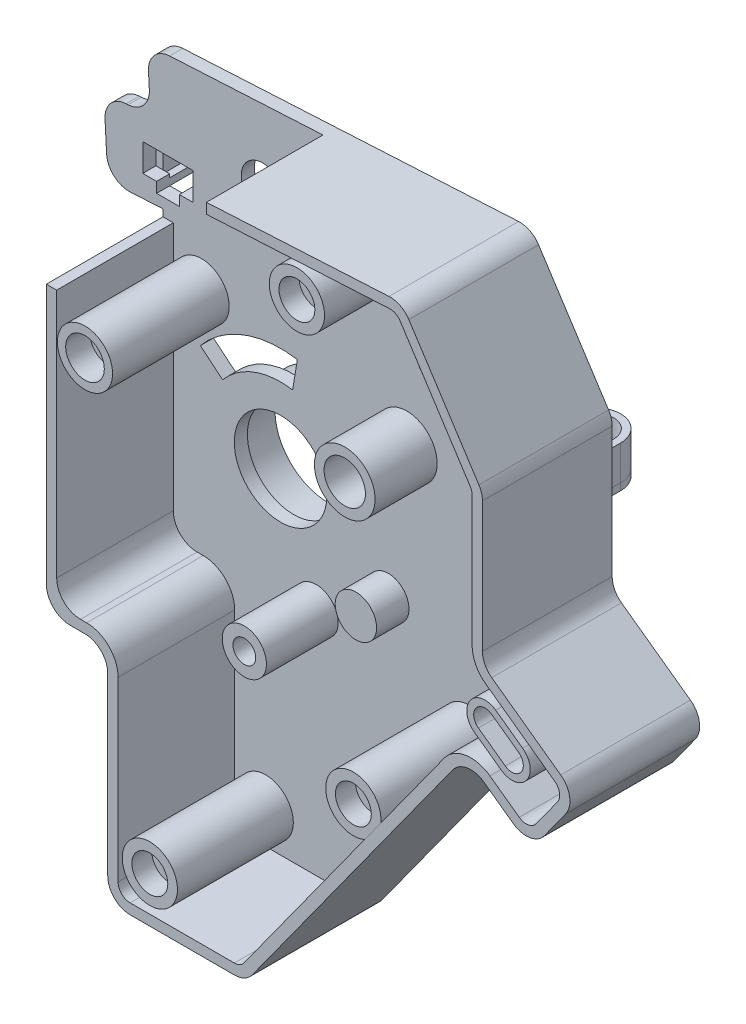
SolidWorks part; units mm, degrees
ref_plane "Front Plane" through (0, 0, 0) normal (0, 0, 1) x (1, 0, 0)
ref_plane "Top Plane" through (0, 0, 0) normal (0, 1, 0) x (1, 0, 0)
ref_plane "Right Plane" through (0, 0, 0) normal (1, 0, 0) x (0, 0, -1)
sketch "Sketch1" plane through (0, 0, 0) normal (0, 0, 1) x (1, 0, 0)
  line L34 (3.24, 0) -> (18.3427, 0)
  line L35 (20.9699, 1.3438) -> (49.9994, 41.5647)
  line L36 (54.5228, 42.2957) -> (58.7717, 39.229)
  line L37 (63.2951, 39.96) -> (66.3851, 44.2413)
  line L38 (65.6541, 48.7647) -> (55.6621, 55.9765)
  line L39 (54.3183, 58.6037) -> (54.3183, 77.4885)
  line L40 (53.7975, 79.2503) -> (43.6473, 94.916)
  line L41 (0, 3.24) -> (0, 32)
  line L48 (-11.1707, 93.6047) -> (40.7546, 96.3896)
  line L49 (0, 32) -> (-8.9, 32)
  line L50 (-8.9, 32) -> (-8.9, 59.47)
  line L54 (-11.1707, 93.6047) -> (-10.6994, 84.8173)
  line L55 (-10.6994, 84.8173) -> (-17.4697, 84.4542)
  line L56 (-17.4697, 84.4542) -> (-16.8913, 73.6697)
  line L57 (-8.9, 59.47) -> (-8.9, 74.0983)
  line L58 (-8.9, 74.0983) -> (-16.8913, 73.6697)
  arc A2 (3.24, 0) -> (0, 3.24) centre (3.24, 3.24) cw
  arc A3 (18.3427, 0) -> (20.9699, 1.3438) centre (18.3427, 3.24) ccw
  arc A4 (49.9994, 41.5647) -> (54.5228, 42.2957) centre (52.6266, 39.6685) cw
  arc A5 (58.7717, 39.229) -> (63.2951, 39.96) centre (60.6679, 41.8562) ccw
  arc A6 (66.3851, 44.2413) -> (65.6541, 48.7647) centre (63.758, 46.1375) ccw
  arc A7 (55.6621, 55.9765) -> (54.3183, 58.6037) centre (57.5583, 58.6037) cw
  arc A8 (54.3183, 77.4885) -> (53.7975, 79.2503) centre (51.0783, 77.4885) ccw
  arc A9 (43.6473, 94.916) -> (40.7546, 96.3896) centre (40.9282, 93.1543) ccw
  point P24 (0, 0)
  point P27 (20, 0)
  point P30 (51.8956, 44.1918)
  point P33 (61.3989, 37.3328)
  point P36 (68.2813, 46.8685)
  point P39 (54.3183, 56.9464)
  point P42 (54.3183, 78.4464)
  point P45 (42.6275, 96.49)
  dimension "D5" = 11.76
  dimension "D13" = 10.8
  dimension "D18" = 8.9
  dimension "D20" = 8.0028
  dimension "D1" = 20
  dimension "D2" = 54.5
  dimension "D3" = 125.82
  dimension "D4" = 11.72
  dimension "D6" = 17.22
  dimension "D7" = 21.5
  dimension "D8" = 21.5
  dimension "D9" = 32
  dimension "D10" = 27.47
  dimension "D12" = 8.8
  dimension "D14" = 119.87
  dimension "D15" = 52
  dimension "D16" = 147.06
  dimension "D19" = 6.78
extrude "Boss-Extrude1" add sketch "Sketch1" along normal blind 1.9
sketch "Sketch16" plane through (0, 0, 1.9) normal (0, 0, 1) x (1, 0, 0)
  line L0 (-15.8915, 83.0367) -> (-15.4738, 75.2479)
  line L1 (-15.4738, 75.2479) -> (-7.4, 75.6809)
  line L2 (-7.4, 75.6809) -> (-7.4, 33.5)
  line L3 (-7.4, 33.5) -> (1.5, 33.5)
  line L4 (1.5, 33.5) -> (1.5, 3.24)
  line L5 (3.24, 1.5) -> (18.3427, 1.5)
  line L6 (19.7536, 2.2217) -> (48.7832, 42.4425)
  line L7 (55.4007, 43.512) -> (59.6496, 40.4453)
  line L8 (62.0788, 40.8379) -> (65.1689, 45.1192)
  line L9 (64.7763, 47.5484) -> (54.7843, 54.7602)
  line L10 (52.8183, 58.6037) -> (52.8183, 77.4885)
  line L11 (52.5386, 78.4346) -> (42.3884, 94.1004)
  line L12 (40.835, 94.8918) -> (-9.5925, 92.1872)
  line L13 (-9.5925, 92.1872) -> (-9.1213, 83.3998)
  line L14 (-9.1213, 83.3998) -> (-15.8915, 83.0367)
  line L15 (-8.9, 74.0983) -> (-8.9, 32)
  line L16 (-8.9, 32) -> (0, 32)
  line L17 (0, 32) -> (0, 3.24)
  line L18 (3.24, 0) -> (18.3427, 0)
  line L19 (20.9699, 1.3438) -> (49.9994, 41.5647)
  line L20 (54.5228, 42.2957) -> (58.7717, 39.229)
  line L21 (63.2951, 39.96) -> (66.3851, 44.2413)
  line L22 (65.6541, 48.7647) -> (55.6621, 55.9765)
  line L23 (54.3183, 58.6037) -> (54.3183, 77.4885)
  line L24 (53.7975, 79.2503) -> (43.6473, 94.916)
  line L25 (40.7546, 96.3896) -> (-11.1707, 93.6047)
  line L26 (-11.1707, 93.6047) -> (-10.6994, 84.8173)
  line L27 (-10.6994, 84.8173) -> (-17.4697, 84.4542)
  line L28 (-17.4697, 84.4542) -> (-16.8913, 73.6697)
  line L29 (-16.8913, 73.6697) -> (-8.9, 74.0983)
  line L30 (-8.9, 74.0983) -> (-8.9, 32)
  line L31 (-8.9, 32) -> (0, 32)
  line L32 (0, 32) -> (0, 3.24)
  line L33 (3.24, 0) -> (18.3427, 0)
  line L34 (20.9699, 1.3438) -> (49.9994, 41.5647)
  line L35 (54.5228, 42.2957) -> (58.7717, 39.229)
  line L36 (63.2951, 39.96) -> (66.3851, 44.2413)
  line L37 (65.6541, 48.7647) -> (55.6621, 55.9765)
  line L38 (54.3183, 58.6037) -> (54.3183, 77.4885)
  line L39 (53.7975, 79.2503) -> (43.6473, 94.916)
  line L40 (40.7546, 96.3896) -> (-11.1707, 93.6047)
  line L41 (-11.1707, 93.6047) -> (-10.6994, 84.8173)
  line L42 (-10.6994, 84.8173) -> (-17.4697, 84.4542)
  line L43 (-17.4697, 84.4542) -> (-16.8913, 73.6697)
  line L44 (-16.8913, 73.6697) -> (-8.9, 74.0983)
  arc A0 (1.5, 3.24) -> (3.24, 1.5) centre (3.24, 3.24) ccw
  arc A1 (18.3427, 1.5) -> (19.7536, 2.2217) centre (18.3427, 3.24) ccw
  arc A2 (55.4007, 43.512) -> (48.7832, 42.4425) centre (52.6266, 39.6685) ccw
  arc A3 (59.6496, 40.4453) -> (62.0788, 40.8379) centre (60.6679, 41.8562) ccw
  arc A4 (65.1689, 45.1192) -> (64.7763, 47.5484) centre (63.758, 46.1375) ccw
  arc A5 (52.8183, 58.6037) -> (54.7843, 54.7602) centre (57.5583, 58.6037) ccw
  arc A6 (52.8183, 77.4885) -> (52.5386, 78.4346) centre (51.0783, 77.4885) ccw
  arc A7 (42.3884, 94.1004) -> (40.835, 94.8918) centre (40.9282, 93.1543) ccw
  arc A8 (0, 3.24) -> (3.24, 0) centre (3.24, 3.24) ccw
  arc A9 (18.3427, 0) -> (20.9699, 1.3438) centre (18.3427, 3.24) ccw
  arc A10 (54.5228, 42.2957) -> (49.9994, 41.5647) centre (52.6266, 39.6685) ccw
  arc A11 (58.7717, 39.229) -> (63.2951, 39.96) centre (60.6679, 41.8562) ccw
  arc A12 (66.3851, 44.2413) -> (65.6541, 48.7647) centre (63.758, 46.1375) ccw
  arc A13 (54.3183, 58.6037) -> (55.6621, 55.9765) centre (57.5583, 58.6037) ccw
  arc A14 (54.3183, 77.4885) -> (53.7975, 79.2503) centre (51.0783, 77.4885) ccw
  arc A15 (43.6473, 94.916) -> (40.7546, 96.3896) centre (40.9282, 93.1543) ccw
  arc A16 (0, 3.24) -> (3.24, 0) centre (3.24, 3.24) ccw
  arc A17 (18.3427, 0) -> (20.9699, 1.3438) centre (18.3427, 3.24) ccw
  arc A18 (54.5228, 42.2957) -> (49.9994, 41.5647) centre (52.6266, 39.6685) ccw
  arc A19 (58.7717, 39.229) -> (63.2951, 39.96) centre (60.6679, 41.8562) ccw
  arc A20 (66.3851, 44.2413) -> (65.6541, 48.7647) centre (63.758, 46.1375) ccw
  arc A21 (54.3183, 58.6037) -> (55.6621, 55.9765) centre (57.5583, 58.6037) ccw
  arc A22 (54.3183, 77.4885) -> (53.7975, 79.2503) centre (51.0783, 77.4885) ccw
  arc A23 (43.6473, 94.916) -> (40.7546, 96.3896) centre (40.9282, 93.1543) ccw
  dimension "D1" = 0
  dimension "D2" = 1.5
extrude "Boss-Extrude8" add sketch "Sketch16" along normal blind 16.9
sketch "Sketch6" plane through (0, 0, 1.9) normal (0, 0, 1) x (1, 0, 0)
  circle A0 centre (6, 6.5) radius 4
  circle A1 centre (6, 6.5) radius 2.6
  circle A2 centre (35.5, 30) radius 4
  circle A3 centre (35.5, 30) radius 2.6
  circle A4 centre (27.32, 89.23) radius 4
  circle A7 centre (27.32, 89.23) radius 2.6
  dimension "D3" = 8
  dimension "D4" = 5.2
  dimension "D7" = 8
  dimension "D8" = 5.2
  dimension "D11" = 8
  dimension "D12" = 5.2
  dimension "D2" = 6
  dimension "D1" = 6.5
  dimension "D5" = 35.5
  dimension "D6" = 30
  dimension "D9" = 27.32
  dimension "D10" = 89.23
extrude "Boss-Extrude3" add sketch "Sketch6" along normal blind 16.8
sketch "Sketch8" plane through (0, 0, 1.9) normal (0, 0, 1) x (1, 0, 0)
  line L0 (10.5808, 64.9132) -> (9.9052, 60.7679)
  line L1 (-0.2479, 56.9644) -> (-3.4809, 59.6455)
  line L3 (-7.55, 63.02) -> (8.15, 50) construction
  line L4 (0, 0) -> (8.15, 50) construction
  line L5 (8.15, 50) -> (10.9104, 66.9353) construction
  line L6 (20.9463, 50) -> (-15.5457, 50) construction
  line L7 (54.3183, 58.6037) -> (54.3183, 77.4885) construction
  circle A0 centre (8.15, 50) radius 6.71
  circle A1 centre (5.55, 83.99) radius 3.1
  arc A2 (9.9052, 60.7679) -> (-0.2479, 56.9644) centre (8.15, 50) ccw
  arc A3 (10.5808, 64.9132) -> (-3.4809, 59.6455) centre (8.15, 50) ccw
  circle A4 centre (32.5683, 75.4) radius 5
  circle A5 centre (35.5, 30) radius 2.6 construction
  point P11 (-7.55, 63.02)
  dimension "D3" = 13.42
  dimension "D6" = 6.2
  dimension "D7" = 4.2
  dimension "D8" = 4.2
  dimension "D10" = 45.4
  dimension "D12" = 10
  dimension "D1" = 50
  dimension "D2" = 8.15
  dimension "D4" = 5.55
  dimension "D5" = 83.99
  dimension "D9" = 15.7
  dimension "D11" = 21.75
  dimension "D13" = 39.669
extrude "Cut-Extrude2" cut sketch "Sketch8" against normal up to surface (1.9 mm away) up to face at (27.395, 52.0581, 0)
sketch "Sketch9" plane through (0, 0, 1.9) normal (0, 0, 1) x (1, 0, 0)
  circle A0 centre (26.45, 62) radius 4.4
  circle A1 centre (26.45, 62) radius 3
  circle A3 centre (26.45, 62) radius 1.375 construction
  dimension "D1" = 8.8
  dimension "D4" = 6
extrude "Boss-Extrude4" add sketch "Sketch9" along normal blind 9
sketch "Sketch10" plane through (0, 0, 1.9) normal (0, 0, 1) x (1, 0, 0)
  circle A0 centre (23.77, 41.68) radius 3
  circle A2 centre (23.77, 41.68) radius 2 construction
  dimension "D1" = 6
extrude "Boss-Extrude5" add sketch "Sketch10" along normal blind 4.7
sketch "Sketch11" plane through (0, 0, 1.9) normal (0, 0, 1) x (1, 0, 0)
  circle A0 centre (13.3, 34.85) radius 3.2
  circle A1 centre (13.3, 34.85) radius 1.65
  circle A3 centre (13.3, 34.85) radius 3 construction
  dimension "D1" = 6.4
  dimension "D4" = 3.3
extrude "Boss-Extrude6" add sketch "Sketch11" along normal blind 10.4
sketch "Sketch12" plane through (0, 0, 1.9) normal (0, 0, 1) x (1, 0, 0)
  circle A0 centre (-3.3, 66.65) radius 4
  dimension "D1" = 8
  dimension "D3" = 3.3
  dimension "D2" = 66.65
extrude "Boss-Extrude7" add sketch "Sketch12" along normal blind 16.9
sketch "Sketch13" plane through (0, 0, 18.8) normal (0, 0, 1) x (1, 0, 0)
  circle A0 centre (-3.3, 66.65) radius 2.8
  dimension "D1" = 5.6
extrude "Cut-Extrude3" cut sketch "Sketch13" against normal blind 3.5
sketch "Sketch14" plane through (0, 0, 1.9) normal (0, 0, 1) x (1, 0, 0)
  line L0 (44.25, 71.49) -> (51.55, 71.49)
  line L1 (51.55, 71.49) -> (51.55, 67.49)
  line L2 (51.55, 67.49) -> (49.55, 67.49)
  line L3 (49.55, 67.49) -> (49.55, 65.99)
  line L4 (49.55, 65.99) -> (46.25, 65.99)
  line L5 (46.25, 65.99) -> (46.25, 67.49)
  line L6 (46.25, 67.49) -> (44.25, 67.49)
  line L7 (44.25, 67.49) -> (44.25, 71.49)
  line L8 (-11.82, 81.09) -> (-4.52, 81.09)
  line L9 (-4.52, 81.09) -> (-4.52, 77.09)
  line L10 (-4.52, 77.09) -> (-6.52, 77.09)
  line L11 (-6.52, 77.09) -> (-6.52, 75.59)
  line L12 (-6.52, 75.59) -> (-9.82, 75.59)
  line L13 (-9.82, 75.59) -> (-9.82, 77.09)
  line L14 (-9.82, 77.09) -> (-11.82, 77.09)
  line L15 (-11.82, 77.09) -> (-11.82, 81.09)
  dimension "D1" = 2
  dimension "D2" = 2
  dimension "D3" = 46.25
  dimension "D4" = 65.99
  dimension "D5" = 4
  dimension "D6" = 7.3
  dimension "D7" = 5.5
  dimension "D8" = 7.3
  dimension "D9" = 6.52
  dimension "D10" = 75.59
  dimension "D11" = 4
  dimension "D12" = 5.5
sketch "Sketch17" plane through (0, 0, 18.8) normal (0, 0, 1) x (1, 0, 0)
  line L0 (-8.9, 73.0983) -> (-7.4, 73.0983)
  line L1 (-8.9, 74.0983) -> (-8.9, 32) construction
  line L2 (-7.4, 75.6809) -> (-7.4, 33.5) construction
  line L3 (40.7546, 96.3896) -> (-11.1707, 93.6047) construction
  line L4 (40.835, 94.8918) -> (-9.5925, 92.1872) construction
  line L5 (-11.1707, 93.6047) -> (-10.6994, 84.8173) construction
  line L6 (-17.4697, 84.4542) -> (-16.8913, 73.6697) construction
  line L7 (-10.6994, 84.8173) -> (-17.4697, 84.4542) construction
  line L8 (-9.5925, 92.1872) -> (-9.1213, 83.3998) construction
  line L9 (-9.1213, 83.3998) -> (-15.8915, 83.0367) construction
  line L10 (-15.8915, 83.0367) -> (-15.4738, 75.2479) construction
  line L11 (-15.4738, 75.2479) -> (-7.4, 75.6809) construction
  line L12 (10.7977, 94.7829) -> (-11.1707, 93.6047)
  line L13 (10.7977, 93.2808) -> (-9.5925, 92.1872)
  line L14 (-11.1707, 93.6047) -> (-10.6994, 84.8173)
  line L15 (-17.4697, 84.4542) -> (-16.8913, 73.6697)
  line L16 (-10.6994, 84.8173) -> (-17.4697, 84.4542)
  line L17 (-9.5925, 92.1872) -> (-9.1213, 83.3998)
  line L18 (-9.1213, 83.3998) -> (-15.8915, 83.0367)
  line L19 (-15.8915, 83.0367) -> (-15.4738, 75.2479)
  line L20 (-15.4738, 75.2479) -> (-7.4, 75.6809)
  line L21 (-7.4, 75.6809) -> (-7.4, 73.0983)
  line L22 (-16.8913, 73.6697) -> (-8.9, 74.0983) construction
  line L23 (-8.9, 74.0983) -> (-8.9, 73.0983)
  line L24 (-16.8913, 73.6697) -> (-8.9, 74.0983)
  line L25 (10.7977, 94.7829) -> (10.7977, 93.2808)
  point P4 (10.7977, 94.7829)
  dimension "D1" = 1
  dimension "D2" = 30
extrude "Cut-Extrude4" cut sketch "Sketch17" against normal blind 16.9
fillet "Fillet1" radius 3.24 1 edges at (-17.4697, 84.4542, 0.95)
fillet "Fillet2" radius 3.24 1 edges at (-10.6994, 84.8173, 0.95)
fillet "Fillet3" radius 3.24 1 edges at (-11.1707, 93.6047, 0.95)
fillet "Fillet4" radius 3.24 1 edges at (-16.8913, 73.6697, 0.95)
fillet "Fillet7" radius 3.45 1 edges at (-8.9, 32, 9.4)
fillet "Fillet8" radius 3.45 1 edges at (-7.4, 33.5, 10.35)
fillet "Fillet9" radius 4.56 1 edges at (1.5, 33.5, 10.35)
fillet "Fillet10" radius 3.33 1 edges at (0, 32, 9.4)
extrude "Cut-Extrude8" cut sketch "Sketch14" against normal blind 10
sketch "Sketch19" plane through (0, 65.99, 0) normal (0, 1, 0) x (1, 0, 0)
  line L0 (46.25, 4) -> (46.25, 0)
  line L1 (49.55, 4) -> (49.55, 0)
  line L2 (44.25, 4) -> (44.25, 0)
  line L3 (51.55, 4) -> (51.55, 0)
  line L4 (44.25, 0) -> (46.25, 0)
  line L5 (49.55, 0) -> (51.55, 0)
  arc A0 (49.55, 4) -> (46.25, 4) centre (47.9, 4) ccw
  arc A1 (51.55, 4) -> (44.25, 4) centre (47.9, 4) ccw
  dimension "D1" = 4
  dimension "D2" = 7.3
extrude "Boss-Extrude9" add sketch "Sketch19" along normal blind 1
sketch "Sketch20" plane through (0, 66.99, 0) normal (0, 1, 0) x (1, 0, 0)
  line L0 (44.25, 0) -> (46.25, 0) construction
  line L1 (49.55, 0) -> (51.55, 0) construction
  line L2 (51.55, 0) -> (51.55, 4) construction
  line L3 (44.25, 4) -> (44.25, 0) construction
  line L4 (44.25, 0) -> (45.25, 0)
  line L5 (50.55, 0) -> (51.55, 0)
  line L6 (51.55, 0) -> (51.55, 4)
  line L7 (44.25, 4) -> (44.25, 0)
  line L8 (45.25, 4) -> (45.25, 0)
  line L9 (50.55, 4) -> (50.55, 0)
  arc A1 (51.55, 4) -> (44.25, 4) centre (47.9, 4) ccw construction
  arc A2 (50.55, 4) -> (45.25, 4) centre (47.9, 4) ccw
  arc A3 (50.55, 4) -> (45.25, 4) centre (47.9, 4) ccw
  arc A4 (51.55, 4) -> (44.25, 4) centre (47.9, 4) ccw
  dimension "D1" = 1
extrude "Boss-Extrude10" add sketch "Sketch20" along normal blind 5 separate body
sketch "Sketch21" plane through (0, 75.59, 0) normal (0, 1, 0) x (1, 0, 0)
  line L0 (-9.82, 4) -> (-9.82, 0)
  line L1 (-6.52, 4) -> (-6.52, 0)
  line L2 (-11.82, 4) -> (-11.82, 0)
  line L3 (-4.52, 4) -> (-4.52, 0)
  line L4 (-11.82, 0) -> (-9.82, 0)
  line L5 (-6.52, 0) -> (-4.52, 0)
  arc A0 (-6.52, 4) -> (-9.82, 4) centre (-8.17, 4) ccw
  arc A1 (-4.52, 4) -> (-11.82, 4) centre (-8.17, 4) ccw
  dimension "D1" = 7.3
  dimension "D2" = 4
extrude "Boss-Extrude11" add sketch "Sketch21" along normal blind 1
sketch "Sketch22" plane through (0, 76.59, 0) normal (0, 1, 0) x (1, 0, 0)
  line L0 (-11.82, 0) -> (-9.82, 0) construction
  line L1 (-6.52, 0) -> (-4.52, 0) construction
  line L2 (-4.52, 0) -> (-4.52, 4) construction
  line L3 (-11.82, 4) -> (-11.82, 0) construction
  line L4 (-11.82, 0) -> (-10.82, 0)
  line L5 (-5.52, 0) -> (-4.52, 0)
  line L6 (-4.52, 0) -> (-4.52, 4)
  line L7 (-11.82, 4) -> (-11.82, 0)
  line L8 (-10.82, 4) -> (-10.82, 0)
  line L9 (-5.52, 4) -> (-5.52, 0)
  arc A1 (-4.52, 4) -> (-11.82, 4) centre (-8.17, 4) ccw construction
  arc A2 (-5.52, 4) -> (-10.82, 4) centre (-8.17, 4) ccw
  arc A3 (-5.52, 4) -> (-10.82, 4) centre (-8.17, 4) ccw
  arc A4 (-4.52, 4) -> (-11.82, 4) centre (-8.17, 4) ccw
  dimension "D1" = 1
extrude "Boss-Extrude12" add sketch "Sketch22" along normal blind 5 separate body
sketch "Sketch23" plane through (10.7977, 0, 0) normal (-1, 0, 0) x (0, 0, 1)
  line L4 (18.8, 93.2808) -> (18.8, 94.7829)
  line L5 (18.8, 94.7829) -> (1.9, 94.7829)
  line L6 (1.9, 94.7829) -> (1.9, 93.2808)
  line L7 (1.9, 93.2808) -> (18.8, 93.2808)
  line L8 (18.8, 93.2808) -> (18.8, 94.7829)
  line L9 (18.8, 94.7829) -> (1.9, 94.7829)
  line L10 (1.9, 94.7829) -> (1.9, 93.2808)
  line L11 (1.9, 93.2808) -> (18.8, 93.2808)
  dimension "D1" = 0
extrude "Cut-Extrude9" cut sketch "Sketch23" against normal blind 2
sketch "Sketch24" plane through (12.7977, 0, 0) normal (-1, 0, 0) x (0, 0, 1)
  line L4 (18.8, 93.388) -> (18.8, 94.7829)
  line L5 (18.8, 94.7829) -> (1.9, 94.7829)
  line L6 (1.9, 94.7829) -> (1.9, 93.388)
  line L7 (1.9, 93.388) -> (18.8, 93.388)
  line L8 (18.8, 93.388) -> (18.8, 94.7829)
  line L9 (18.8, 94.7829) -> (1.9, 94.7829)
  line L10 (1.9, 94.7829) -> (1.9, 93.388)
  line L11 (1.9, 93.388) -> (18.8, 93.388)
  dimension "D1" = 0
sketch "Sketch25" plane through (0, 0, 18.8) normal (0, 0, 1) x (1, 0, 0)
  line L0 (12.7977, 94.7829) -> (12.7977, 94.8902)
  line L1 (40.7546, 96.3896) -> (10.7977, 94.7829) construction
  line L2 (12.7977, 94.8902) -> (10.7977, 94.7829)
  line L3 (10.7977, 94.7829) -> (12.7977, 94.7829)
extrude "Cut-Extrude11" cut sketch "Sketch25" against normal up to surface (16.9 mm away) up to face at (8.6, 6.5, 1.9)
sketch "Sketch26" plane through (12.7977, 0, 0) normal (-1, 0, 0) x (0, 0, 1)
  line L4 (18.8, 93.388) -> (18.8, 94.8902)
  line L5 (18.8, 94.8902) -> (1.9, 94.8902)
  line L6 (1.9, 94.8902) -> (1.9, 93.388)
  line L7 (1.9, 93.388) -> (18.8, 93.388)
  line L8 (18.8, 93.388) -> (18.8, 95.9949)
  line L9 (18.8, 95.9949) -> (1.9, 95.9949)
  line L10 (1.9, 95.9949) -> (1.9, 93.388)
  line L11 (1.9, 93.388) -> (18.8, 93.388)
  dimension "D1" = 0
extrude "Cut-Extrude12" cut sketch "Sketch26" against normal blind 1.5
sketch "Sketch27" plane through (0, 0, 0) normal (0, 0, -1) x (-1, 0, 0)
  circle A0 centre (-8.15, 50) radius 6.71 construction
  circle A1 centre (-8.15, 50) radius 6.71
  circle A2 centre (-8.15, 50) radius 7.71
  circle A3 centre (-8.15, 50) radius 8.71
  dimension "D1" = 1
  dimension "D2" = 1
extrude "Boss-Extrude13" add sketch "Sketch27" along normal blind 5 contours A3 A2
sketch "Sketch28" plane through (0, 0, 1.9) normal (0, 0, 1) x (1, 0, 0)
  circle A0 centre (6, 6.5) radius 2.6 construction
  circle A1 centre (27.32, 89.23) radius 2.6
  circle A2 centre (27.32, 89.23) radius 2.6
  circle A3 centre (6, 6.5) radius 2.6
  circle A4 centre (35.5, 30) radius 2.6 construction
  circle A5 centre (35.5, 30) radius 2.6
  dimension "D1" = 0
extrude "Cut-Extrude13" cut sketch "Sketch28" against normal blind 10
ref_plane "Plane1" through (0, 0, 15.8) normal (0, 0, 1) x (1, 0, 0)
sketch "Sketch30" plane through (0, 0, 15.8) normal (0, 0, 1) x (1, 0, 0)
  line L0 (37.184, 26.3718) -> (39.474, 29.5445) construction
  line L1 (37.184, 26.3718) -> (39.474, 29.5445)
  circle A1 centre (27.32, 89.23) radius 1.3
  circle A3 centre (6, 6.5) radius 1.3
  circle A5 centre (35.5, 30) radius 1.3
  circle A6 centre (6, 6.5) radius 4 construction
  circle A8 centre (27.32, 89.23) radius 4 construction
  arc A9 (39.474, 29.5445) -> (37.184, 26.3718) centre (35.5, 30) ccw construction
  circle A10 centre (27.32, 89.23) radius 4
  arc A11 (39.474, 29.5445) -> (37.184, 26.3718) centre (35.5, 30) ccw
  circle A12 centre (6, 6.5) radius 4
  dimension "D1" = 2.6
  dimension "D2" = 2.6
  dimension "D3" = 2.6
extrude "Boss-Extrude14" add sketch "Sketch30" against normal blind 1
sketch "Sketch31" plane through (0, 0, 1.9) normal (0, 0, 1) x (1, 0, 0)
  line L0 (54.4948, 49.8264) -> (58.3869, 47.0173) construction
  line L1 (55.4605, 51.1643) -> (59.3526, 48.3552)
  line L2 (53.5292, 48.4885) -> (57.4213, 45.6793)
  line L3 (65.6541, 48.7647) -> (55.6621, 55.9765) construction
  line L4 (63.2951, 39.96) -> (66.3851, 44.2413) construction
  line L5 (56.0457, 51.9752) -> (59.9378, 49.166)
  line L6 (52.9439, 47.6776) -> (56.8361, 44.8685)
  arc A0 (55.4605, 51.1643) -> (53.5292, 48.4885) centre (54.4948, 49.8264) ccw
  arc A1 (57.4213, 45.6793) -> (59.3526, 48.3552) centre (58.3869, 47.0173) ccw
  arc A2 (56.8361, 44.8685) -> (59.9378, 49.166) centre (58.3869, 47.0173) ccw
  arc A3 (56.0457, 51.9752) -> (52.9439, 47.6776) centre (54.4948, 49.8264) ccw
  point P2 (56.4409, 48.4218)
  dimension "D1" = 1.65
  dimension "D2" = 4.02
  dimension "D3" = 8.11
  dimension "D4" = 4.8
  dimension "D5" = 1
extrude "Boss-Extrude15" add sketch "Sketch31" along normal blind 16.7
sketch "Sketch32" plane through (0, 0, 1.9) normal (0, 0, 1) x (1, 0, 0)
  line L2 (53.5292, 48.4885) -> (57.4213, 45.6793)
  line L3 (59.3526, 48.3552) -> (55.4605, 51.1643)
  line L4 (53.5292, 48.4885) -> (57.4213, 45.6793)
  line L5 (59.3526, 48.3552) -> (55.4605, 51.1643)
  arc A2 (57.4213, 45.6793) -> (59.3526, 48.3552) centre (58.3869, 47.0173) ccw
  arc A3 (55.4605, 51.1643) -> (53.5292, 48.4885) centre (54.4948, 49.8264) ccw
  arc A4 (57.4213, 45.6793) -> (59.3526, 48.3552) centre (58.3869, 47.0173) ccw
  arc A5 (55.4605, 51.1643) -> (53.5292, 48.4885) centre (54.4948, 49.8264) ccw
  dimension "D1" = 0
extrude "Boss-Extrude16" add sketch "Sketch32" along normal blind 12.13
